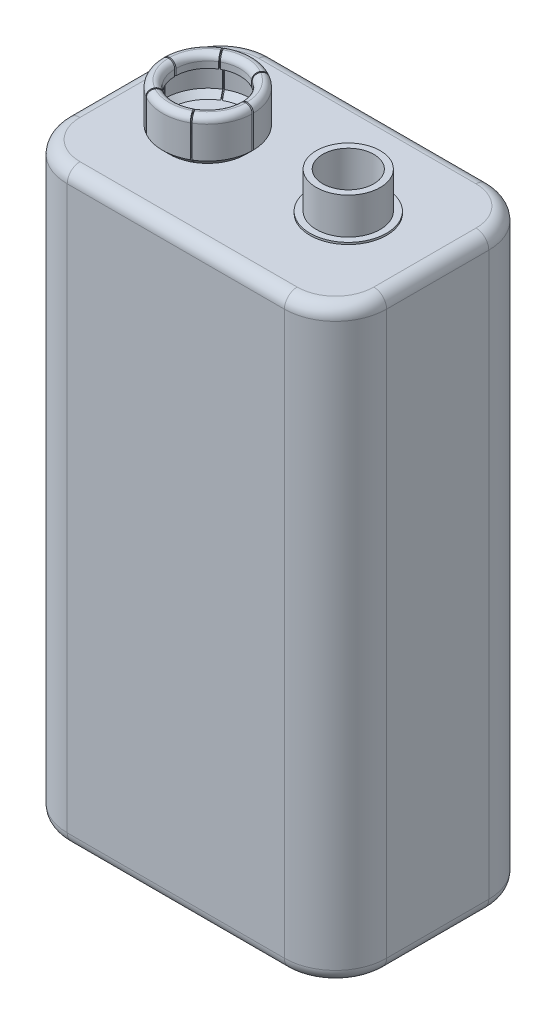
SolidWorks part; units mm, degrees
ref_plane "Front Plane" through (0, 0, 0) normal (0, 0, 1) x (1, 0, 0)
ref_plane "Top Plane" through (0, 0, 0) normal (0, 1, 0) x (1, 0, 0)
ref_plane "Right Plane" through (0, 0, 0) normal (1, 0, 0) x (0, 0, -1)
sketch "Sketch2" plane through (0, 0, 0) normal (0, 1, 0) x (1, 0, 0)
  line L1 (-12.5, -8) -> (12.5, -8)
  line L2 (-12.5, -8) -> (-12.5, 8)
  line L3 (-12.5, 8) -> (12.5, 8)
  line L4 (12.5, -8) -> (12.5, 8)
  line L5 (-12.5, -8) -> (12.5, 8) construction
  line L6 (-12.5, 8) -> (12.5, -8) construction
  point P0 (0, 0)
  dimension "D1" = 25
  dimension "D2" = 16
extrude "Boss-Extrude1" add sketch "Sketch2" along normal blind 46
fillet "Fillet1" radius 4 4 edges at (-12.5, 23, -8) (-12.5, 23, 8) (12.5, 23, -8) (12.5, 23, 8)
fillet "Fillet2" radius 1 16 edges at (-11.3284, 0, 6.8284) (0, 0, 8) (11.3284, 0, 6.8284) (12.5, 0, 0) (11.3284, 0, -6.8284) (0, 0, -8) (-11.3284, 0, -6.8284) (-12.5, 0, 0) (11.3284, 46, -6.8284) (12.5, 46, 0) (11.3284, 46, 6.8284) (0, 46, 8) (-11.3284, 46, 6.8284) (-12.5, 46, 0) (-11.3284, 46, -6.8284) (0, 46, -8)
sketch "Sketch3" plane through (0, 46, 0) normal (0, 1, 0) x (1, 0, 0)
  circle A0 centre (5.5, 0) radius 2.5
  dimension "D1" = 5
  dimension "D2" = 5.5
sketch "Sketch6" plane through (0, 46, 0) normal (0, 1, 0) x (1, 0, 0)
  circle A0 centre (-5.5, 0) radius 1
  circle A1 centre (5.5, 0) radius 1
  dimension "D1" = 2
  dimension "D2" = 2
  dimension "D3" = 11
  dimension "D4" = 5.5
extrude "Extrude-Thin1" add sketch "Sketch3" along normal blind 3 thin thin type one direction reverse wall 0.5
extrude "Boss-Extrude2" add sketch "Sketch6" along normal blind 0.75
ref_axis "Axis1" through (-5.5, 46.75, 0) along (0, -1, 0)
sketch "Sketch9" plane through (0, 0, 0) normal (0, 0, 1) x (1, 0, 0)
  line L0 (-4.5, 46) -> (-2.5, 46)
  line L2 (-2.5, 46) -> (-1.9697, 46.5303)
  line L3 (-1.9697, 46.5303) -> (-1.9697, 49.0303)
  line L5 (-2.9642, 49.0303) -> (-2.9642, 48.5352)
  arc A0 (-2.4691, 49.5255) -> (-2.9642, 49.0303) centre (-2.4691, 49.0303) ccw
  arc A1 (-1.9697, 49.0303) -> (-2.4691, 49.5255) centre (-2.4648, 49.0303) ccw
  dimension "D1" = 2
  dimension "D2" = 2.5
  dimension "D3" = 0.75
revolve "Revolve-Thin1" add sketch "Sketch9" angle 360 about axis through (-5.5, 46.75, 0) along (0, -1, 0) wall 0.15
sketch "Sketch10" plane through (0, 46.15, 0) normal (0, 1, 0) x (1, 0, 0)
  line L1 (-3.2191, -0.05) -> (-1.7191, -0.05)
  line L2 (-3.2191, -0.05) -> (-3.2191, 0.05)
  line L3 (-3.2191, 0.05) -> (-1.7191, 0.05)
  line L4 (-1.7191, -0.05) -> (-1.7191, 0.05)
  line L5 (-3.2191, -0.05) -> (-1.7191, 0.05) construction
  line L6 (-3.2191, 0.05) -> (-1.7191, -0.05) construction
  circle A0 centre (-5.5, 0) radius 3.0309 construction
  point P0 (-2.4691, 0)
  dimension "D1" = 0.1
  dimension "D2" = 1.5
extrude "Cut-Extrude1" cut sketch "Sketch10" along normal through all
pattern_circular "CirPattern1" count 6 over 360 about axis through (-5.5, 0, 0) along (0, 1, 0) of "Cut-Extrude1"
sketch "Sketch11" plane through (0, 46, 0) normal (0, 1, 0) x (1, 0, 0)
  circle A0 centre (5.5, 0) radius 3
  dimension "D1" = 6
extrude "Boss-Extrude3" add sketch "Sketch11" along normal blind 0.15
